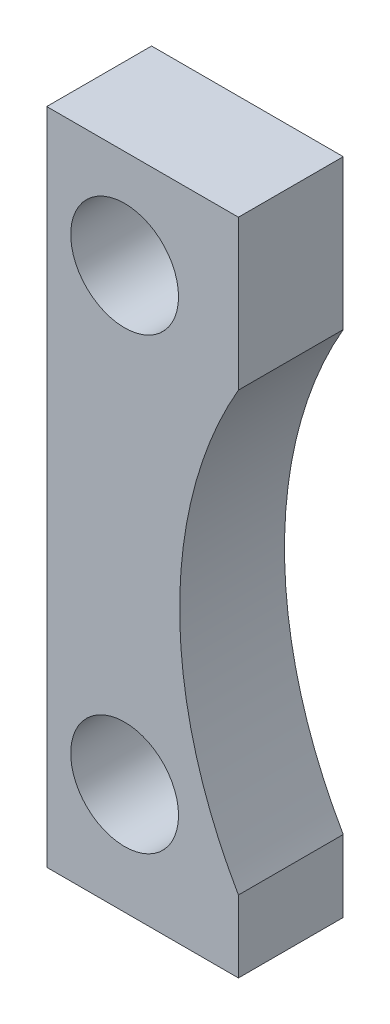
SolidWorks part; units mm, degrees
ref_plane "Front Plane" through (0, 0, 0) normal (0, 0, 1) x (1, 0, 0)
ref_plane "Top Plane" through (0, 0, 0) normal (0, 1, 0) x (1, 0, 0)
ref_plane "Right Plane" through (0, 0, 0) normal (1, 0, 0) x (0, 0, -1)
sketch "Çizim1" plane through (0, 0, 0) normal (0, 0, 1) x (1, 0, 0)
  line L0 (0, 0) -> (0, 110)
  line L1 (0, 110) -> (32, 110)
  line L2 (32, 110) -> (32, 85)
  line L3 (0, 0) -> (32, 0)
  line L4 (32, 0) -> (32, 12)
  arc A0 (32, 12) -> (32, 85) centre (95, 48.5) cw
  dimension "D1" = 110
  dimension "D2" = 32
  dimension "D3" = 25
  dimension "D4" = 12
  dimension "D5" = 95
extrude "Yükseklik-Ekstrüzyon1" add sketch "Çizim1" along normal mid plane 17.5
sketch "Çizim2" plane through (0, 0, 8.75) normal (0, 0, 1) x (1, 0, 0)
  line L0 (0, 110) -> (0, 0) construction
  line L1 (32, 110) -> (0, 110) construction
  line L2 (0, 0) -> (32, 0) construction
  circle A0 centre (13, 93.5) radius 9
  circle A1 centre (13, 18.5) radius 9
  dimension "D1" = 18
  dimension "D2" = 13
  dimension "D3" = 16.5
  dimension "D4" = 18.5
  dimension "D5" = 13
extrude "Kes-Ekstrüzyon1" cut sketch "Çizim2" against normal through all
